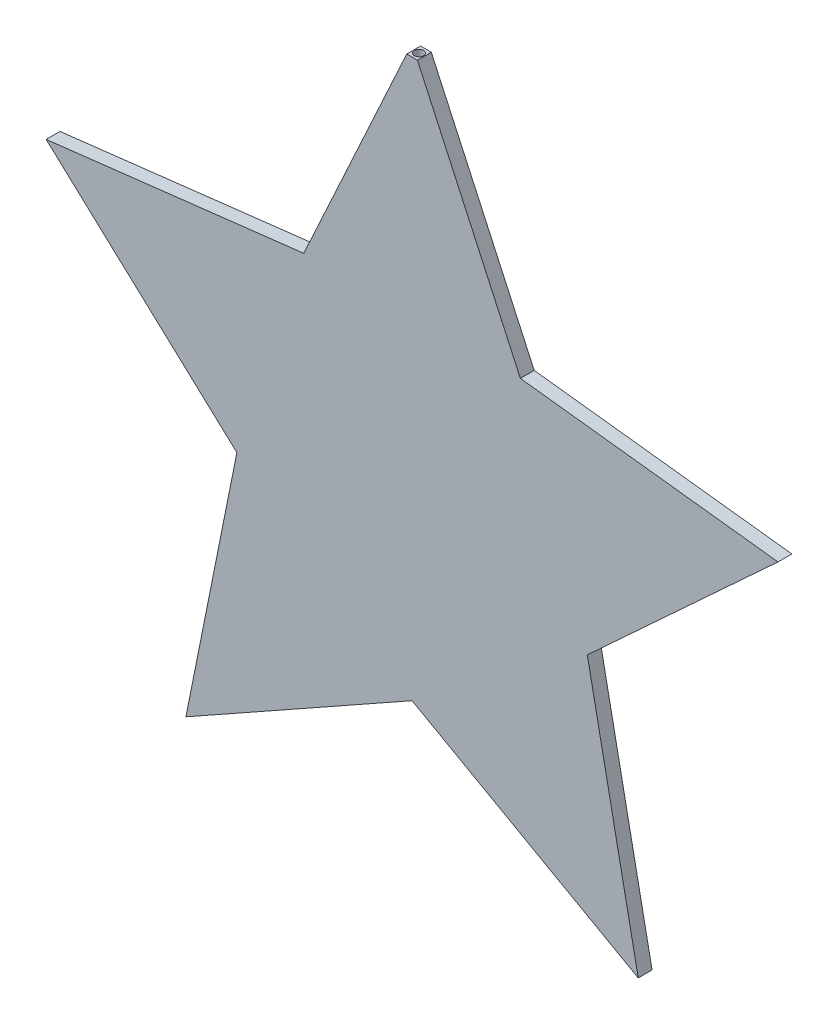
SolidWorks part; units mm, degrees
ref_plane "Front Plane" through (0, 0, 0) normal (0, 0, 1) x (1, 0, 0)
ref_plane "Top Plane" through (0, 0, 0) normal (0, 1, 0) x (1, 0, 0)
ref_plane "Right Plane" through (0, 0, 0) normal (1, 0, 0) x (0, 0, -1)
sketch "Sketch1" plane through (0, 0, 0) normal (0, 0, 1) x (1, 0, 0)
  line L0 (-49.0416, 0) -> (0, 27.5496)
  line L1 (0, 150.9346) -> (-79.351, 93.2827) construction
  line L2 (-79.351, 93.2827) -> (-49.0416, 0) construction
  line L3 (-49.0416, 0) -> (49.0416, 0) construction
  line L4 (49.0416, 0) -> (79.351, 93.2827) construction
  line L5 (79.351, 93.2827) -> (0, 150.9346) construction
  line L6 (0, 27.5496) -> (49.0416, 0)
  line L7 (-79.351, 93.2827) -> (-37.9951, 55.1547)
  line L8 (-37.9951, 55.1547) -> (-49.0416, 0)
  line L9 (0, 150.9346) -> (-23.4822, 99.8205)
  line L10 (-23.4822, 99.8205) -> (-79.351, 93.2827)
  line L11 (79.351, 93.2827) -> (23.4822, 99.8205)
  line L12 (23.4822, 99.8205) -> (0, 150.9346)
  line L13 (49.0416, 0) -> (37.9951, 55.1547)
  line L14 (37.9951, 55.1547) -> (79.351, 93.2827)
  circle A0 centre (0, 67.5) radius 67.5 construction
  point P4 (0, 0)
  point P23 (0, 67.5)
  dimension "D1" = 135
  dimension "D2" = 56.25
  dimension "D3" = 5
extrude "Boss-Extrude1" add sketch "Sketch1" along normal mid plane 3
sketch "Sketch3" plane through (0, 0, 0) normal (0, 1, 0) x (1, 0, 0)
  circle A0 centre (0, 0) radius 1
  dimension "D1" = 2
extrude "Cut-Extrude1" cut sketch "Sketch3" along normal blind 217
sketch "Sketch4" plane through (0, 0, 0) normal (0, 0, 1) x (1, 0, 0)
  line L0 (-1.6348, 148.4159) -> (1.9293, 148.4159)
  line L1 (-1.6348, 148.4159) -> (0, 151.9706)
  line L2 (0, 151.9706) -> (1.9293, 148.4159)
extrude "Cut-Extrude2" cut sketch "Sketch4" against normal mid plane 10
